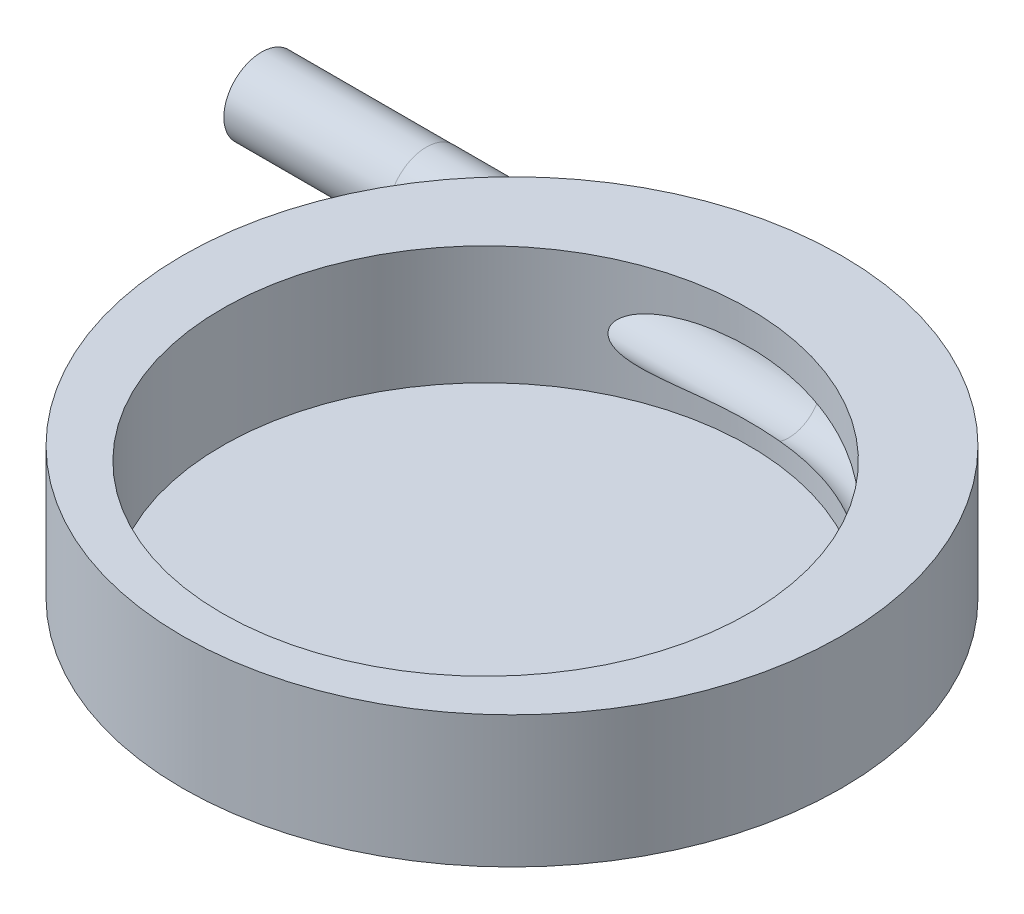
SolidWorks part; units mm, degrees
material "PLA"
ref_plane "Front Plane" through (0, 0, 0) normal (0, 0, 1) x (1, 0, 0)
ref_plane "Top Plane" through (0, 0, 0) normal (0, 1, 0) x (1, 0, 0)
ref_plane "Right Plane" through (0, 0, 0) normal (1, 0, 0) x (0, 0, -1)
sketch "Sketch1" plane through (0, 0, 0) normal (0, 1, 0) x (1, 0, 0)
  circle A0 centre (0, 0) radius 50
  circle A1 centre (0, -4) radius 40
  dimension "D1" = 4
  dimension "D2" = 80
extrude "Boss-Extrude1" add sketch "Sketch1" along normal blind 20
sketch "Sketch2" plane through (0, 0, 0) normal (0, 1, 0) x (1, 0, 0)
  circle A0 centre (0, 0) radius 50
  circle A1 centre (0, -4) radius 40
  dimension "D1" = 4
extrude "Boss-Extrude2" add sketch "Sketch2" along normal blind 2 and the other way blind 4 contours A1
sketch "Sketch3" plane through (0, 20, 0) normal (0, 1, 0) x (1, 0, 0)
  circle A0 centre (0, 0) radius 50
  circle A1 centre (0, 0) radius 60
  circle A2 centre (0, 55) radius 2.2
  circle A3 centre (55, 0) radius 2.2
  circle A4 centre (0, -55) radius 2.2
  circle A5 centre (-55, 0) radius 2.2
  point P15 (0, 0)
  dimension "D1" = 55
  dimension "D2" = 4
extrude "Boss-Extrude3" [suppressed] add sketch "Sketch3" along normal blind 5 separate body
ref_plane "Plane1" through (-50, 0, 0) normal (-1, 0, 0) x (0, 0, 1)
sketch "Sketch4" plane through (-50, 0, 0) normal (-1, 0, 0) x (0, 0, 1)
  circle A0 centre (-37, 10) radius 4.75
  circle A1 centre (-37, 10) radius 5.75
  dimension "D1" = 9.5
  dimension "D2" = 11.5
  dimension "D3" = 10
  dimension "D4" = 37
sketch "Sketch5" plane through (0, 0, 0) normal (0, 1, 0) x (1, 0, 0)
  line L0 (-50, 37) -> (-20.0985, 37)
  line L2 (-50, 41.75) -> (-50, 32.25) construction
sweep "Sweep1" add profiles "Sketch4" path "Sketch5"
sketch "Sketch6" plane through (0, 0, 0) normal (0, 1, 0) x (1, 0, 0)
  line L0 (-50, 41) -> (5, 41)
  line L1 (-50, 11) -> (-50, -11) construction
  arc A0 (5, 41) -> (33.5816, -28.002) centre (5, 0.5795) cw
  dimension "D1" = 135
  dimension "D2" = 55
  dimension "D3" = 41
sketch "Sketch7" plane through (-50, 0, 0) normal (-1, 0, 0) x (0, 0, 1)
  circle A0 centre (-37, 10.0538) radius 5
  dimension "D1" = 37
sweep "Cut-Sweep4" cut profiles "Sketch7" path "Sketch6"
sketch "Sketch8" plane through (-50, 0, 0) normal (-1, 0, 0) x (0, 0, 1)
  circle A0 centre (-36.9889, 10.0296) radius 4.9733
  circle A1 centre (-36.9889, 10.0296) radius 5.7184
extrude "Boss-Extrude4" add sketch "Sketch8" along normal blind 25
